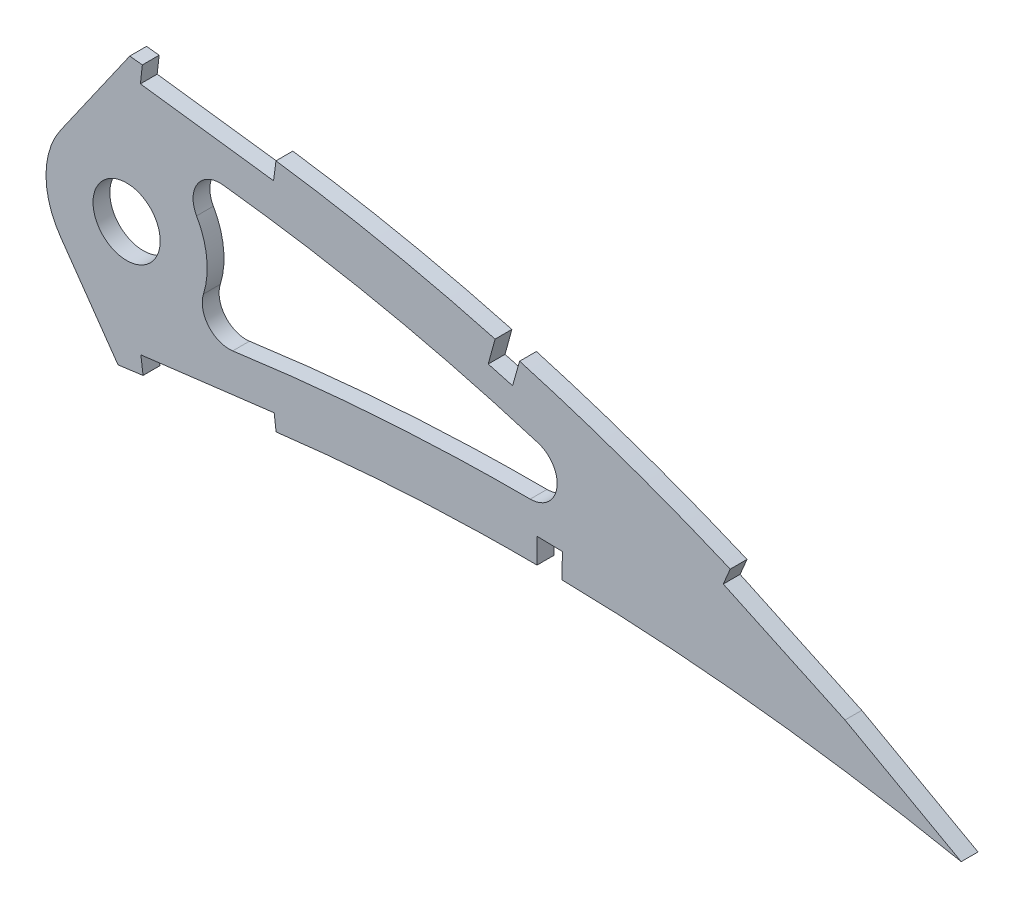
SolidWorks part; units mm, degrees
ref_plane "Front Plane" through (0, 0, 0) normal (0, 0, 1) x (1, 0, 0)
ref_plane "Top Plane" through (0, 0, 0) normal (0, 1, 0) x (1, 0, 0)
ref_plane "Right Plane" through (0, 0, 0) normal (1, 0, 0) x (0, 0, -1)
curve "Curve1"
  spline degree 3 poles (0, 0, 0) (0.1249, -0.5894, 0) (0.3751, -1.7709, 0) (1.0551, -3.4717, 0) (1.9543, -5.1067, 0) (3.0917, -6.6716, 0) (4.4597, -8.1658, 0) (6.0551, -9.5909, 0) (7.8766, -10.9463, 0) (9.9217, -12.2312, 0) (12.1874, -13.447, 0) (14.6712, -14.593, 0) (17.3708, -15.6688, 0) (20.2833, -16.6729, 0) (23.4051, -17.607, 0) (26.7332, -18.4687, 0) (30.2639, -19.2592, 0) (33.9938, -19.9766, 0) (37.9188, -20.6214, 0) (42.0348, -21.1935, 0) (46.3376, -21.6931, 0) (50.823, -22.1192, 0) (55.4866, -22.4726, 0) (60.3236, -22.7538, 0) (65.3294, -22.9634, 0) (70.4993, -23.1008, 0) (75.828, -23.1681, 0) (81.3109, -23.1662, 0) (86.9426, -23.0948, 0) (92.7182, -22.9577, 0) (98.6323, -22.754, 0) (104.6794, -22.4863, 0) (110.8541, -22.1572, 0) (117.1509, -21.7679, 0) (123.5642, -21.32, 0) (130.0885, -20.8172, 0) (136.7178, -20.2607, 0) (143.4464, -19.6538, 0) (150.2683, -18.9994, 0) (157.1776, -18.2998, 0) (164.1682, -17.5581, 0) (171.2339, -16.7767, 0) (178.3687, -15.9599, 0) (185.566, -15.1091, 0) (192.8198, -14.2292, 0) (200.1233, -13.3218, 0) (207.4703, -12.3905, 0) (214.8542, -11.4396, 0) (222.2681, -10.469, 0) (229.7058, -9.4856, 0) (237.1601, -8.4887, 0) (244.6246, -7.4833, 0) (252.0922, -6.4726, 0) (259.5558, -5.4569, 0) (267.0088, -4.4404, 0) (274.4442, -3.4259, 0) (281.8548, -2.4135, 0) (289.2339, -1.4081, 0) (296.574, -0.4098, 0) (303.8684, 0.5795, 0) (311.1101, 1.5569, 0) (318.2922, 2.521, 0) (325.4074, 3.4714, 0) (332.4485, 4.4082, 0) (339.3029, 5.3032, 0) (345.9529, 6.204, 0) (352.4207, 6.9424, 0) (358.808, 7.5727, 0) (365.1214, 8.0894, 0) (371.3533, 8.5001, 0) (377.4966, 8.8075, 0) (383.544, 9.0161, 0) (389.4878, 9.132, 0) (395.3205, 9.1582, 0) (401.0343, 9.1029, 0) (406.6218, 8.9708, 0) (412.075, 8.7675, 0) (417.3864, 8.5002, 0) (422.5485, 8.1759, 0) (427.5535, 7.7996, 0) (432.3944, 7.38, 0) (437.0637, 6.9232, 0) (441.5544, 6.4344, 0) (445.8598, 5.924, 0) (449.973, 5.3952, 0) (453.8879, 4.8568, 0) (457.5982, 4.3142, 0) (461.0979, 3.7743, 0) (464.3817, 3.2423, 0) (467.4441, 2.7253, 0) (470.2803, 2.228, 0) (472.8856, 1.7553, 0) (475.2562, 1.3133, 0) (477.3874, 0.904, 0) (479.2765, 0.5343, 0) (480.9199, 0.2058, 0) (482.3151, -0.077, 0) (483.4599, -0.3128, 0) (484.3523, -0.4979, 0) (484.9907, -0.6325, 0) (485.3743, -0.7125, 0) (485.5448, -0.7489, 0) (485.5874, -0.758, 0) knots 0 0 0 0 0.003638 0.007293 0.011028 0.014901 0.018963 0.023258 0.027821 0.032679 0.037853 0.043362 0.049215 0.055422 0.061989 0.068918 0.076211 0.083868 0.091887 0.100266 0.109 0.118085 0.127515 0.137285 0.147388 0.157816 0.168563 0.179619 0.190977 0.202627 0.21456 0.226767 0.239236 0.251959 0.264924 0.27812 0.291536 0.30516 0.318981 0.332985 0.347163 0.361499 0.375981 0.390597 0.405333 0.420175 0.43511 0.450124 0.465203 0.480333 0.495501 0.51069 0.525887 0.541078 0.556247 0.571382 0.586466 0.601485 0.616424 0.631269 0.646007 0.660621 0.675098 0.689423 0.703582 0.716908 0.730009 0.742952 0.755726 0.76832 0.780724 0.792927 0.804916 0.816679 0.828204 0.839475 0.850481 0.861208 0.871639 0.881763 0.891564 0.901027 0.910139 0.918884 0.927249 0.935221 0.942785 0.949928 0.956638 0.962904 0.968712 0.974054 0.978918 0.983297 0.98718 0.990561 0.993433 0.995791 0.99763 0.998946 0.999737 1 1 1 1
curve "Curve2"
  spline degree 3 poles (486.1938, 0.758, 0) (486.1565, 0.781, 0) (486.0077, 0.8729, 0) (485.6723, 1.0786, 0) (485.1139, 1.4213, 0) (484.3321, 1.8984, 0) (483.3276, 2.5088, 0) (482.0999, 3.2482, 0) (480.6498, 4.1141, 0) (478.9775, 5.1026, 0) (477.0833, 6.2089, 0) (474.9678, 7.4286, 0) (472.6313, 8.7548, 0) (470.0748, 10.182, 0) (467.2989, 11.7035, 0) (464.3043, 13.3123, 0) (461.0921, 15.0004, 0) (457.6635, 16.7605, 0) (454.019, 18.5827, 0) (450.1605, 20.4596, 0) (446.0892, 22.3819, 0) (441.8065, 24.3391, 0) (437.3149, 26.3234, 0) (432.6155, 28.3224, 0) (427.7112, 30.3274, 0) (422.6039, 32.3272, 0) (417.2967, 34.3124, 0) (411.7916, 36.2703, 0) (406.0928, 38.1924, 0) (400.203, 40.0661, 0) (394.1264, 41.8812, 0) (387.8666, 43.626, 0) (381.4288, 45.2916, 0) (374.8171, 46.8658, 0) (368.037, 48.3381, 0) (361.0939, 49.6996, 0) (353.9938, 50.9366, 0) (346.7562, 52.0484, 0) (339.4976, 52.9732, 0) (332.2539, 53.8802, 0) (325.021, 54.7322, 0) (317.6998, 55.5482, 0) (310.2971, 56.3235, 0) (302.8205, 57.0556, 0) (295.2774, 57.7415, 0) (287.6757, 58.3791, 0) (280.0227, 58.9648, 0) (272.3266, 59.4977, 0) (264.5949, 59.9731, 0) (256.8359, 60.3907, 0) (249.0573, 60.7475, 0) (241.2675, 61.0411, 0) (233.4745, 61.2698, 0) (225.6865, 61.4312, 0) (217.912, 61.5245, 0) (210.159, 61.547, 0) (202.4359, 61.4984, 0) (194.7508, 61.377, 0) (187.1122, 61.1811, 0) (179.5282, 60.9103, 0) (172.0069, 60.5649, 0) (164.5567, 60.1418, 0) (157.1855, 59.6438, 0) (149.9016, 59.0688, 0) (142.713, 58.4167, 0) (135.6273, 57.6901, 0) (128.6522, 56.887, 0) (121.7954, 56.0099, 0) (115.0642, 55.0603, 0) (108.4663, 54.0378, 0) (102.0087, 52.9453, 0) (95.6983, 51.784, 0) (89.542, 50.5572, 0) (83.5463, 49.2652, 0) (77.7176, 47.912, 0) (72.062, 46.4999, 0) (66.5855, 45.0315, 0) (61.2937, 43.5103, 0) (56.192, 41.9397, 0) (51.2862, 40.3215, 0) (46.5802, 38.6618, 0) (42.0796, 36.9619, 0) (37.788, 35.2268, 0) (33.7103, 33.4591, 0) (29.8497, 31.6641, 0) (26.2104, 29.8437, 0) (22.7951, 28.0033, 0) (19.6072, 26.1454, 0) (16.6497, 24.2737, 0) (13.924, 22.3929, 0) (11.4337, 20.504, 0) (9.1798, 18.612, 0) (7.1636, 16.7197, 0) (5.388, 14.8284, 0) (3.8531, 12.9414, 0) (2.5606, 11.0602, 0) (1.511, 9.1866, 0) (0.7066, 7.3219, 0) (0.1466, 5.4673, 0) (-0.16, 3.6254, 0) (-0.2363, 1.7948, 0) (-0.0786, 0.5974, 0) (0, 0, 0) knots 0 0 0 0 0.000254 0.001015 0.002283 0.004057 0.006331 0.009105 0.012374 0.016134 0.02038 0.025106 0.030306 0.035972 0.0421 0.048678 0.055702 0.06316 0.071046 0.07935 0.088063 0.097176 0.106678 0.116562 0.126814 0.137428 0.148394 0.1597 0.171338 0.183298 0.19557 0.208144 0.221012 0.234162 0.247587 0.261277 0.275223 0.289414 0.303771 0.317689 0.331784 0.34604 0.360444 0.374983 0.38964 0.404403 0.419257 0.434187 0.449177 0.464215 0.479284 0.49437 0.509458 0.524532 0.539579 0.554583 0.56953 0.584403 0.599191 0.613877 0.628447 0.642889 0.657186 0.671326 0.685294 0.699078 0.712665 0.726043 0.739198 0.752118 0.764792 0.777208 0.789356 0.801224 0.812804 0.824083 0.835055 0.84571 0.856038 0.866034 0.875689 0.884998 0.893953 0.902553 0.910789 0.918661 0.926166 0.933303 0.940071 0.946475 0.952518 0.958205 0.963547 0.968557 0.97325 0.977651 0.981787 0.985694 0.989415 0.993001 0.996508 1 1 1 1
sketch "Sketch1" plane through (0, 0, 0) normal (0, 0, 1) x (1, 0, 0)
  line L10 (468.8346, -0.7318) -> (473.2376, -1.6265)
  line L24 (469.4201, 0.7318) -> (473.2376, -1.6265)
  spline S4 degree 3 poles (0, 0) (0.1205, -0.5691) (0.3622, -1.7098) (1.0187, -3.352) (1.8869, -4.9306) (2.9851, -6.4414) (4.3058, -7.8841) (5.8462, -9.26) (7.6049, -10.5686) (9.5794, -11.8092) (11.7669, -12.9831) (14.165, -14.0895) (16.7715, -15.1282) (19.5835, -16.0977) (22.5976, -16.9996) (25.8109, -17.8315) (29.2198, -18.5948) (32.821, -19.2874) (36.6106, -19.91) (40.5846, -20.4623) (44.739, -20.9447) (49.0696, -21.3561) (53.5723, -21.6973) (58.2424, -21.9688) (63.0756, -22.1712) (68.067, -22.3038) (73.212, -22.3688) (78.5057, -22.367) (83.9431, -22.298) (89.5194, -22.1656) (95.2294, -21.969) (101.0679, -21.7105) (107.0296, -21.3928) (113.1092, -21.0169) (119.3012, -20.5845) (125.6004, -20.099) (132.0011, -19.5617) (138.4975, -18.9757) (145.0841, -18.344) (151.755, -17.6684) (158.5044, -16.9523) (165.3264, -16.1979) (172.215, -15.4093) (179.164, -14.5879) (186.1676, -13.7383) (193.219, -12.8622) (200.3125, -11.963) (207.4417, -11.0449) (214.5998, -10.1078) (221.781, -9.1584) (228.9781, -8.1958) (236.185, -7.2252) (243.395, -6.2493) (250.6011, -5.2687) (257.797, -4.2872) (264.9759, -3.3077) (272.1308, -2.3302) (279.2553, -1.3596) (286.3422, -0.3957) (293.3849, 0.5595) (300.3768, 1.5032) (307.3111, 2.434) (314.1808, 3.3516) (320.979, 4.2562) (327.597, 5.1203) (334.0175, 5.99) (340.2622, 6.7029) (346.4291, 7.3114) (352.5247, 7.8103) (358.5416, 8.2068) (364.473, 8.5037) (370.3117, 8.7051) (376.0504, 8.817) (381.682, 8.8422) (387.1987, 8.7889) (392.5933, 8.6613) (397.8584, 8.4651) (402.9866, 8.2069) (407.9706, 7.8939) (412.8029, 7.5305) (417.4768, 7.1254) (421.985, 6.6843) (426.3208, 6.2125) (430.4776, 5.7196) (434.449, 5.2091) (438.2288, 4.6893) (441.8111, 4.1654) (445.1901, 3.6441) (448.3605, 3.1305) (451.3172, 2.6312) (454.0557, 2.1511) (456.571, 1.6948) (458.8598, 1.268) (460.9176, 0.8728) (462.7415, 0.5159) (464.3281, 0.1987) (465.6753, -0.0743) (466.7805, -0.302) (467.6421, -0.4807) (468.2585, -0.6106) (468.6289, -0.688) (468.7935, -0.7231) (468.8346, -0.7318) knots 0 0 0 0 0.003638 0.007293 0.011028 0.014901 0.018963 0.023258 0.027821 0.032679 0.037853 0.043362 0.049215 0.055422 0.061989 0.068918 0.076211 0.083868 0.091887 0.100266 0.109 0.118085 0.127515 0.137285 0.147388 0.157816 0.168563 0.179619 0.190977 0.202627 0.21456 0.226767 0.239236 0.251959 0.264924 0.27812 0.291536 0.30516 0.318981 0.332985 0.347163 0.361499 0.375981 0.390597 0.405333 0.420175 0.43511 0.450124 0.465203 0.480333 0.495501 0.51069 0.525887 0.541078 0.556247 0.571382 0.586466 0.601485 0.616424 0.631269 0.646007 0.660621 0.675098 0.689423 0.703582 0.716908 0.730009 0.742952 0.755726 0.76832 0.780724 0.792927 0.804916 0.816679 0.828204 0.839475 0.850481 0.861208 0.871639 0.881763 0.891564 0.901027 0.910139 0.918884 0.927249 0.935221 0.942785 0.949928 0.956638 0.962904 0.968712 0.974054 0.978918 0.983297 0.98718 0.990561 0.993433 0.995791 0.99763 0.998946 0.999737 1 1 1 1
  spline S5 degree 3 poles (469.4201, 0.7318) (469.3841, 0.7541) (469.2404, 0.8428) (468.9167, 1.0414) (468.3775, 1.3722) (467.6227, 1.8329) (466.6528, 2.4222) (465.4675, 3.1361) (464.0673, 3.9722) (462.4528, 4.9266) (460.6239, 5.9947) (458.5814, 7.1723) (456.3256, 8.4527) (453.8572, 9.8307) (451.1771, 11.2997) (448.2858, 12.8531) (445.1844, 14.4829) (441.8741, 16.1822) (438.3554, 17.9416) (434.63, 19.7538) (430.6991, 21.6097) (426.5642, 23.4994) (422.2275, 25.4152) (417.6903, 27.3453) (412.9551, 29.2812) (408.024, 31.2119) (402.8999, 33.1286) (397.5848, 35.019) (392.0826, 36.8747) (386.396, 38.6838) (380.5291, 40.4363) (374.4852, 42.1209) (368.2695, 43.7291) (361.8859, 45.2489) (355.3397, 46.6704) (348.6362, 47.9849) (341.781, 49.1793) (334.7931, 50.2527) (327.7849, 51.1456) (320.7912, 52.0213) (313.8078, 52.844) (306.7391, 53.6318) (299.5919, 54.3803) (292.3732, 55.0872) (285.0903, 55.7494) (277.7509, 56.365) (270.362, 56.9305) (262.9313, 57.445) (255.4664, 57.9041) (247.975, 58.3072) (240.4649, 58.6517) (232.9437, 58.9352) (225.4196, 59.156) (217.9004, 59.3118) (210.394, 59.4019) (202.9085, 59.4236) (195.4518, 59.3767) (188.0319, 59.2595) (180.6568, 59.0703) (173.3345, 58.8089) (166.0727, 58.4754) (158.8795, 58.0669) (151.7626, 57.5861) (144.73, 57.031) (137.7894, 56.4013) (130.9481, 55.6998) (124.2137, 54.9244) (117.5934, 54.0775) (111.0945, 53.1607) (104.7242, 52.1735) (98.4894, 51.1187) (92.3968, 49.9974) (86.4528, 48.8129) (80.6639, 47.5656) (75.0363, 46.259) (69.5758, 44.8957) (64.2883, 43.4779) (59.1791, 42.0092) (54.2533, 40.4928) (49.5168, 38.9304) (44.9732, 37.328) (40.6279, 35.6867) (36.4843, 34.0115) (32.5473, 32.3048) (28.8199, 30.5716) (25.3061, 28.8141) (22.0087, 27.0372) (18.9307, 25.2434) (16.0753, 23.4363) (13.4436, 21.6203) (11.0393, 19.7967) (8.8631, 17.9699) (6.9165, 16.1429) (5.2022, 14.3168) (3.7201, 12.4949) (2.4723, 10.6786) (1.4589, 8.8696) (0.6822, 7.0693) (0.1415, 5.2787) (-0.1545, 3.5004) (-0.2281, 1.7329) (-0.0759, 0.5768) (0, 0) knots 0 0 0 0 0.000254 0.001015 0.002283 0.004057 0.006331 0.009105 0.012374 0.016134 0.02038 0.025106 0.030306 0.035972 0.0421 0.048678 0.055702 0.06316 0.071046 0.07935 0.088063 0.097176 0.106678 0.116562 0.126814 0.137428 0.148394 0.1597 0.171338 0.183298 0.19557 0.208144 0.221012 0.234162 0.247587 0.261277 0.275223 0.289414 0.303771 0.317689 0.331784 0.34604 0.360444 0.374983 0.38964 0.404403 0.419257 0.434187 0.449177 0.464215 0.479284 0.49437 0.509458 0.524532 0.539579 0.554583 0.56953 0.584403 0.599191 0.613877 0.628447 0.642889 0.657186 0.671326 0.685294 0.699078 0.712665 0.726043 0.739198 0.752118 0.764792 0.777208 0.789356 0.801224 0.812804 0.824083 0.835055 0.84571 0.856038 0.866034 0.875689 0.884998 0.893953 0.902553 0.910789 0.918661 0.926166 0.933303 0.940071 0.946475 0.952518 0.958205 0.963547 0.968557 0.97325 0.977651 0.981787 0.985694 0.989415 0.993001 0.996508 1 1 1 1
extrude "Boss-Extrude1" add sketch "Sketch1" along normal blind 3.175
sketch "Sketch3" plane through (0, 0, 0) normal (0, 0, -1) x (-1, 0, 0)
  circle A1 centre (-305.6931, 26.2554) radius 6.35
extrude "Cut-Extrude2" cut sketch "Sketch3" against normal blind 7.62
sketch "Sketch5" plane through (0, 0, 3.175) normal (0, 0, 1) x (1, 0, 0)
  line L0 (293.2092, 17.5141) -> (304.0729, 1.9991)
  line L1 (293.2092, 34.9967) -> (306.2863, 53.6727)
  line L2 (305.6931, 26.2554) -> (349.5919, 26.2554) construction
  line L3 (183.9003, -14.0121) -> (182.6717, -3.9267)
  circle A0 centre (305.6931, 26.2554) radius 6.35 construction
  circle A1 centre (305.6931, 26.2554) radius 6.35
  circle A2 centre (305.6931, 26.2554) radius 15.24
  arc A3 (318.9225, 33.8212) -> (323.9632, 41.3838) centre (323.3323, 36.3431) cw
  spline S0 degree 3 poles (-2902.693, -753.8532) (64.3326, 64.9902) (-8.1305, 19.5334) (1.0187, -3.352) (1.8869, -4.9306) (2.9851, -6.4414) (4.3058, -7.8841) (5.8462, -9.26) (7.6049, -10.5686) (9.5794, -11.8092) (11.7669, -12.9831) (14.165, -14.0895) (16.7715, -15.1282) (19.5835, -16.0977) (22.5976, -16.9996) (25.8109, -17.8315) (29.2198, -18.5948) (32.821, -19.2874) (36.6106, -19.91) (40.5846, -20.4623) (44.739, -20.9447) (49.0696, -21.3561) (53.5723, -21.6973) (58.2424, -21.9688) (63.0756, -22.1712) (68.067, -22.3038) (73.212, -22.3688) (78.5057, -22.367) (83.9431, -22.298) (89.5194, -22.1656) (95.2294, -21.969) (101.0679, -21.7105) (107.0296, -21.3928) (113.1092, -21.0169) (119.3012, -20.5845) (125.6004, -20.099) (132.0011, -19.5617) (138.4975, -18.9757) (145.0841, -18.344) (151.755, -17.6684) (158.5044, -16.9523) (165.3264, -16.1979) (172.215, -15.4093) (179.164, -14.5879) (186.1676, -13.7383) (193.219, -12.8622) (200.3125, -11.963) (207.4417, -11.0449) (214.5998, -10.1078) (221.781, -9.1584) (228.9781, -8.1958) (236.185, -7.2252) (243.395, -6.2493) (250.6011, -5.2687) (257.797, -4.2872) (264.9759, -3.3077) (272.1308, -2.3302) (279.2553, -1.3596) (286.3422, -0.3957) (293.3849, 0.5595) (300.3768, 1.5032) (307.3111, 2.434) (314.1808, 3.3516) (320.979, 4.2562) (327.597, 5.1203) (334.0175, 5.99) (340.2622, 6.7029) (346.4291, 7.3114) (352.5247, 7.8103) (358.5416, 8.2068) (364.473, 8.5037) (370.3117, 8.7051) (376.0504, 8.817) (381.682, 8.8422) (387.1987, 8.7889) (392.5933, 8.6613) (397.8584, 8.4651) (402.9866, 8.2069) (407.9706, 7.8939) (412.8029, 7.5305) (417.4768, 7.1254) (421.985, 6.6843) (426.3208, 6.2125) (430.4776, 5.7196) (434.449, 5.2091) (438.2288, 4.6893) (441.8111, 4.1654) (445.1901, 3.6441) (448.3605, 3.1305) (451.3172, 2.6312) (454.0557, 2.1511) (456.571, 1.6948) (458.8598, 1.268) (460.9176, 0.8728) (462.7415, 0.5159) (464.3281, 0.1987) (465.6753, -0.0743) (466.7805, -0.302) (467.6421, -0.4807) (468.2585, -0.6106) (485.1734, -4.1411) (500.3081, -15.0737) (1138.8689, 2922.4145) knots -0.14266 -0.14266 -0.14266 -0.14266 0.003638 0.007293 0.011028 0.014901 0.018963 0.023258 0.027821 0.032679 0.037853 0.043362 0.049215 0.055422 0.061989 0.068918 0.076211 0.083868 0.091887 0.100266 0.109 0.118085 0.127515 0.137285 0.147388 0.157816 0.168563 0.179619 0.190977 0.202627 0.21456 0.226767 0.239236 0.251959 0.264924 0.27812 0.291536 0.30516 0.318981 0.332985 0.347163 0.361499 0.375981 0.390597 0.405333 0.420175 0.43511 0.450124 0.465203 0.480333 0.495501 0.51069 0.525887 0.541078 0.556247 0.571382 0.586466 0.601485 0.616424 0.631269 0.646007 0.660621 0.675098 0.689423 0.703582 0.716908 0.730009 0.742952 0.755726 0.76832 0.780724 0.792927 0.804916 0.816679 0.828204 0.839475 0.850481 0.861208 0.871639 0.881763 0.891564 0.901027 0.910139 0.918884 0.927249 0.935221 0.942785 0.949928 0.956638 0.962904 0.968712 0.974054 0.978918 0.983297 0.98718 0.990561 0.993433 0.995791 0.99763 0.998946 0.999737 1.105873 1.105873 1.105873 1.105873 only from (0, 0) to (468.8346, -0.7318) construction
  spline S1 degree 3 poles (2090.3861, 2523.8057) (498.034, -24.8249) (485.355, -9.0416) (468.9167, 1.0414) (468.3775, 1.3722) (467.6227, 1.8329) (466.6528, 2.4222) (465.4675, 3.1361) (464.0673, 3.9722) (462.4528, 4.9266) (460.6239, 5.9947) (458.5814, 7.1723) (456.3256, 8.4527) (453.8572, 9.8307) (451.1771, 11.2997) (448.2858, 12.8531) (445.1844, 14.4829) (441.8741, 16.1822) (438.3554, 17.9416) (434.63, 19.7538) (430.6991, 21.6097) (426.5642, 23.4994) (422.2275, 25.4152) (417.6903, 27.3453) (412.9551, 29.2812) (408.024, 31.2119) (402.8999, 33.1286) (397.5848, 35.019) (392.0826, 36.8747) (386.396, 38.6838) (380.5291, 40.4363) (374.4852, 42.1209) (368.2695, 43.7291) (361.8859, 45.2489) (355.3397, 46.6704) (348.6362, 47.9849) (341.781, 49.1793) (334.7931, 50.2527) (327.7849, 51.1456) (320.7912, 52.0213) (313.8078, 52.844) (306.7391, 53.6318) (299.5919, 54.3803) (292.3732, 55.0872) (285.0903, 55.7494) (277.7509, 56.365) (270.362, 56.9305) (262.9313, 57.445) (255.4664, 57.9041) (247.975, 58.3072) (240.4649, 58.6517) (232.9437, 58.9352) (225.4196, 59.156) (217.9004, 59.3118) (210.394, 59.4019) (202.9085, 59.4236) (195.4518, 59.3767) (188.0319, 59.2595) (180.6568, 59.0703) (173.3345, 58.8089) (166.0727, 58.4754) (158.8795, 58.0669) (151.7626, 57.5861) (144.73, 57.031) (137.7894, 56.4013) (130.9481, 55.6998) (124.2137, 54.9244) (117.5934, 54.0775) (111.0945, 53.1607) (104.7242, 52.1735) (98.4894, 51.1187) (92.3968, 49.9974) (86.4528, 48.8129) (80.6639, 47.5656) (75.0363, 46.259) (69.5758, 44.8957) (64.2883, 43.4779) (59.1791, 42.0092) (54.2533, 40.4928) (49.5168, 38.9304) (44.9732, 37.328) (40.6279, 35.6867) (36.4843, 34.0115) (32.5473, 32.3048) (28.8199, 30.5716) (25.3061, 28.8141) (22.0087, 27.0372) (18.9307, 25.2434) (16.0753, 23.4363) (13.4436, 21.6203) (11.0393, 19.7967) (8.8631, 17.9699) (6.9165, 16.1429) (5.2022, 14.3168) (3.7201, 12.4949) (2.4723, 10.6786) (1.4589, 8.8696) (0.6822, 7.0693) (0.1415, 5.2787) (-0.1545, 3.5004) (-1.1792, -21.0837) (82.4553, -39.7887) (-2988.3522, -254.715) knots -0.11364 -0.11364 -0.11364 -0.11364 0.000254 0.001015 0.002283 0.004057 0.006331 0.009105 0.012374 0.016134 0.02038 0.025106 0.030306 0.035972 0.0421 0.048678 0.055702 0.06316 0.071046 0.07935 0.088063 0.097176 0.106678 0.116562 0.126814 0.137428 0.148394 0.1597 0.171338 0.183298 0.19557 0.208144 0.221012 0.234162 0.247587 0.261277 0.275223 0.289414 0.303771 0.317689 0.331784 0.34604 0.360444 0.374983 0.38964 0.404403 0.419257 0.434187 0.449177 0.464215 0.479284 0.49437 0.509458 0.524532 0.539579 0.554583 0.56953 0.584403 0.599191 0.613877 0.628447 0.642889 0.657186 0.671326 0.685294 0.699078 0.712665 0.726043 0.739198 0.752118 0.764792 0.777208 0.789356 0.801224 0.812804 0.824083 0.835055 0.84571 0.856038 0.866034 0.875689 0.884998 0.893953 0.902553 0.910789 0.918661 0.926166 0.933303 0.940071 0.946475 0.952518 0.958205 0.963547 0.968557 0.97325 0.977651 0.981787 0.985694 0.989415 0.993001 0.996508 1.136643 1.136643 1.136643 1.136643 only from (469.4201, 0.7318) to (0, 0) construction
  spline S2 degree 3 poles (183.9003, -14.0121) (184.6503, -13.9208) (187.7521, -13.5414) (193.219, -12.8622) (200.3125, -11.963) (207.4417, -11.0449) (214.5998, -10.1078) (221.781, -9.1584) (228.9781, -8.1958) (236.185, -7.2252) (243.395, -6.2493) (250.6011, -5.2687) (257.797, -4.2872) (264.9759, -3.3077) (272.1308, -2.3302) (279.2553, -1.3596) (286.3422, -0.3957) (293.3849, 0.5595) (300.3768, 1.5032) (307.3111, 2.434) (314.1808, 3.3516) (320.979, 4.2562) (327.597, 5.1203) (334.0175, 5.99) (340.2622, 6.7029) (346.4291, 7.3114) (352.5247, 7.8103) (358.5416, 8.2068) (364.473, 8.5037) (370.3117, 8.7051) (376.0504, 8.817) (381.682, 8.8422) (387.1987, 8.7889) (392.5933, 8.6613) (397.8584, 8.4651) (402.9866, 8.2069) (407.9706, 7.8939) (412.8029, 7.5305) (417.4768, 7.1254) (421.985, 6.6843) (426.3208, 6.2125) (430.4776, 5.7196) (434.449, 5.2091) (438.2288, 4.6893) (441.8111, 4.1654) (445.1901, 3.6441) (448.3605, 3.1305) (451.3172, 2.6312) (454.0557, 2.1511) (456.571, 1.6948) (458.8598, 1.268) (460.9176, 0.8728) (462.7415, 0.5159) (464.3281, 0.1987) (465.6753, -0.0743) (466.7805, -0.302) (467.6421, -0.4807) (468.2585, -0.6106) (468.6289, -0.688) (468.7935, -0.7231) (468.8346, -0.7318) knots 0.400599 0.400599 0.400599 0.400599 0.405333 0.420175 0.43511 0.450124 0.465203 0.480333 0.495501 0.51069 0.525887 0.541078 0.556247 0.571382 0.586466 0.601485 0.616424 0.631269 0.646007 0.660621 0.675098 0.689423 0.703582 0.716908 0.730009 0.742952 0.755726 0.76832 0.780724 0.792927 0.804916 0.816679 0.828204 0.839475 0.850481 0.861208 0.871639 0.881763 0.891564 0.901027 0.910139 0.918884 0.927249 0.935221 0.942785 0.949928 0.956638 0.962904 0.968712 0.974054 0.978918 0.983297 0.98718 0.990561 0.993433 0.995791 0.99763 0.998946 0.999737 1 1 1 1
  spline S3 degree 3 poles (469.4201, 0.7318) (469.3841, 0.7541) (469.2404, 0.8428) (468.9167, 1.0414) (468.3775, 1.3722) (467.6227, 1.8329) (466.6528, 2.4222) (465.4675, 3.1361) (464.0673, 3.9722) (462.4528, 4.9266) (460.6239, 5.9947) (458.5814, 7.1723) (456.3256, 8.4527) (453.8572, 9.8307) (451.1771, 11.2997) (448.2858, 12.8531) (445.1844, 14.4829) (441.8741, 16.1822) (438.3554, 17.9416) (434.63, 19.7538) (430.6991, 21.6097) (426.5642, 23.4994) (422.2275, 25.4152) (417.6903, 27.3453) (412.9551, 29.2812) (408.024, 31.2119) (402.8999, 33.1286) (397.5848, 35.019) (392.0826, 36.8747) (386.396, 38.6838) (380.5291, 40.4363) (374.4852, 42.1209) (368.2695, 43.7291) (361.8859, 45.2489) (355.3397, 46.6704) (348.6362, 47.9849) (341.781, 49.1793) (334.7931, 50.2527) (327.7849, 51.1456) (320.7912, 52.0213) (313.8078, 52.844) (306.7391, 53.6318) (299.5919, 54.3803) (292.3732, 55.0872) (285.0903, 55.7494) (277.7509, 56.365) (270.362, 56.9305) (262.9313, 57.445) (255.4664, 57.9041) (247.975, 58.3072) (240.4649, 58.6517) (232.9437, 58.9352) (225.4196, 59.156) (217.9004, 59.3118) (210.394, 59.4019) (202.9085, 59.4236) (195.4518, 59.3767) (188.0319, 59.2595) (180.6568, 59.0703) (173.3345, 58.8089) (166.0727, 58.4754) (159.2196, 58.0862) (154.7892, 57.7903) (152.7567, 57.6447) knots 0 0 0 0 0.000254 0.001015 0.002283 0.004057 0.006331 0.009105 0.012374 0.016134 0.02038 0.025106 0.030306 0.035972 0.0421 0.048678 0.055702 0.06316 0.071046 0.07935 0.088063 0.097176 0.106678 0.116562 0.126814 0.137428 0.148394 0.1597 0.171338 0.183298 0.19557 0.208144 0.221012 0.234162 0.247587 0.261277 0.275223 0.289414 0.303771 0.317689 0.331784 0.34604 0.360444 0.374983 0.38964 0.404403 0.419257 0.434187 0.449177 0.464215 0.479284 0.49437 0.509458 0.524532 0.539579 0.554583 0.56953 0.584403 0.599191 0.613877 0.628447 0.642889 0.655138 0.655138 0.655138 0.655138
  spline S4 degree 1 poles (464.0804, -7.9118) (153.4827, 47.5107) knots 0 0 1 1 construction
  spline S5 degree 3 poles (464.0804, -7.9118) (463.9084, -7.8056) (463.5686, -7.5972) (462.8497, -7.1564) (461.6122, -6.4022) (459.1328, -4.9081) (454.1257, -1.9582) (444.02, 3.7271) (429.2585, 11.2569) (411.0875, 19.2719) (392.4933, 26.2159) (373.5378, 32.0377) (357.4743, 35.9236) (346.1381, 38.1196) (339.6159, 39.2264) (334.73, 39.9834) (329.9896, 40.6256) (325.9219, 41.1384) (322.5615, 41.5596) (319.0714, 41.99) (309.7284, 43.101) (294.6207, 44.7218) (267.7473, 47.0812) (234.0934, 49.0222) (193.6937, 49.5345) (166.873, 48.4701) (153.4827, 47.5107) knots 0 0 0 0 0.00128 0.002559 0.005118 0.010237 0.020473 0.040946 0.081892 0.122838 0.163785 0.204731 0.245677 0.26615 0.276386 0.286623 0.29686 0.306235 0.311353 0.317333 0.327569 0.368515 0.409461 0.491354 0.573246 0.655138 0.655138 0.655138 0.655138
  spline S6 degree 1 poles (182.6717, -3.9267) (470.9542, 9.2046) knots 0 0 1 1 construction
  spline S7 degree 3 poles (182.6717, -3.9267) (194.5091, -2.4847) (218.1451, 0.5709) (247.7517, 4.5938) (271.4533, 7.8324) (289.236, 10.254) (304.0754, 12.253) (314.448, 13.6377) (320.4009, 14.4263) (324.846, 15.007) (329.2502, 15.5993) (333.8416, 16.1949) (338.4296, 16.7169) (347.5733, 17.657) (361.3741, 18.6627) (379.7865, 19.1316) (398.1947, 18.7471) (416.547, 17.5348) (434.817, 15.5306) (449.933, 13.2356) (460.4612, 11.3202) (465.7041, 10.2887) (468.3138, 9.7561) (469.637, 9.482) (470.2826, 9.3459) (470.6409, 9.2711) (470.8525, 9.2263) (470.9542, 9.2046) knots 0.400599 0.400599 0.400599 0.400599 0.475525 0.55045 0.587912 0.625375 0.662837 0.681568 0.690934 0.7003 0.709665 0.719031 0.728397 0.737762 0.775225 0.812687 0.85015 0.887612 0.925075 0.962537 0.981269 0.990634 0.995317 0.997659 0.998829 0.999415 1 1 1 1
  dimension "D1" = 30.48
  dimension "D2" = 55
  dimension "D4" = 5.08
  dimension "D3" = 55
  dimension "D5" = 10.16
extrude "Cut-Extrude3" cut sketch "Sketch5" against normal through all
sketch "Sketch6" plane through (0, 0, 3.175) normal (0, 0, 1) x (1, 0, 0)
  line L0 (333.8851, 49.9971) -> (308.6524, 53.2774)
  line L1 (333.8851, 49.9971) -> (308.6524, 53.2774)
  line L2 (308.6524, 53.2774) -> (308.2979, 50.1226)
  line L3 (308.6524, 53.2774) -> (308.2979, 50.1226)
  line L4 (383.3245, 13.5421) -> (383.2838, 8.7802)
  line L5 (383.3245, 13.5421) -> (383.2838, 8.7802)
  line L6 (388.0855, 13.444) -> (383.3245, 13.5421)
  line L7 (388.0855, 13.444) -> (383.3245, 13.5421)
  line L8 (375.3172, 41.7267) -> (374.061, 37.1333)
  line L9 (375.3172, 41.7267) -> (374.061, 37.1333)
  line L10 (379.9538, 40.4233) -> (375.3172, 41.7267)
  line L11 (379.9538, 40.4233) -> (375.3172, 41.7267)
  line L12 (419.7338, 26.2482) -> (418.4942, 23.3257)
  line L13 (419.7338, 26.2482) -> (418.4942, 23.3257)
  line L14 (442.7439, 15.4969) -> (419.7338, 26.2482)
  line L15 (442.7439, 15.4969) -> (419.7338, 26.2482)
  line L16 (465.25, 3.0159) -> (443.046, 15.3498)
  line L17 (465.25, 3.0159) -> (443.046, 15.3498)
  line L18 (463.7082, 0.2405) -> (465.25, 3.0159)
  line L19 (463.7082, 0.2405) -> (465.25, 3.0159)
  line L20 (441.5043, 12.5743) -> (463.7082, 0.2405)
  line L21 (441.5043, 12.5743) -> (463.7082, 0.2405)
  line L22 (418.4942, 23.3257) -> (441.5043, 12.5743)
  line L23 (418.4942, 23.3257) -> (441.5043, 12.5743)
  line L24 (378.6545, 35.877) -> (379.9538, 40.4233)
  line L25 (378.6545, 35.877) -> (379.9538, 40.4233)
  line L26 (374.061, 37.1333) -> (378.6545, 35.877)
  line L27 (374.061, 37.1333) -> (378.6545, 35.877)
  line L28 (387.988, 8.7117) -> (388.0855, 13.444)
  line L29 (387.988, 8.7117) -> (388.0855, 13.444)
  line L30 (383.2838, 8.7802) -> (387.988, 8.7117)
  line L31 (383.2838, 8.7802) -> (387.988, 8.7117)
  line L32 (333.4762, 46.8486) -> (333.8851, 49.9971)
  line L33 (333.4762, 46.8486) -> (333.8851, 49.9971)
  line L34 (308.2979, 50.1226) -> (333.4762, 46.8486)
  line L35 (308.2979, 50.1226) -> (333.4762, 46.8486)
  line L36 (333.9819, 5.7592) -> (333.5917, 8.9094)
  line L37 (333.9819, 5.7592) -> (333.5917, 8.9094)
  line L38 (308.802, 2.6523) -> (333.9819, 5.7592)
  line L39 (308.802, 2.6523) -> (333.9819, 5.7592)
  line L40 (333.5917, 8.9094) -> (308.3883, 5.8002)
  line L41 (333.5917, 8.9094) -> (308.3883, 5.8002)
  line L42 (308.3883, 5.8002) -> (308.802, 2.6523)
  line L43 (308.3883, 5.8002) -> (308.802, 2.6523)
  line L44 (308.6524, 53.2774) -> (309.1465, 57.6742)
  line L45 (309.1465, 57.6742) -> (334.5121, 54.8236)
  line L46 (334.5121, 54.8236) -> (333.8851, 49.9971)
  line L47 (375.3172, 41.7267) -> (377.2563, 48.8169)
  line L48 (377.2563, 48.8169) -> (381.9524, 47.5326)
  line L49 (381.9524, 47.5326) -> (379.9538, 40.4233)
  line L50 (463.7082, 0.2405) -> (477.0981, -7.1974)
  line L51 (477.0981, -7.1974) -> (481.3618, 0.4784)
  line L52 (481.3618, 0.4784) -> (422.6391, 33.0978)
  line L53 (422.6391, 33.0978) -> (419.7338, 26.2482)
  line L54 (383.2838, 8.7802) -> (383.2314, 2.6526)
  line L55 (383.2314, 2.6526) -> (387.8632, 2.6526)
  line L56 (387.8632, 2.6526) -> (387.988, 8.7117)
  line L57 (308.802, 2.6523) -> (309.3119, -1.4806)
  line L58 (309.3119, -1.4806) -> (334.4919, 1.6263)
  line L59 (334.4919, 1.6263) -> (333.9819, 5.7592)
extrude "Cut-Extrude4" cut sketch "Sketch6" against normal through all
fillet "Fillet1" radius 5.08 2 edges at (414.7297, 17.5573, 1.5875) (314.1868, 13.6018, 1.5875)
